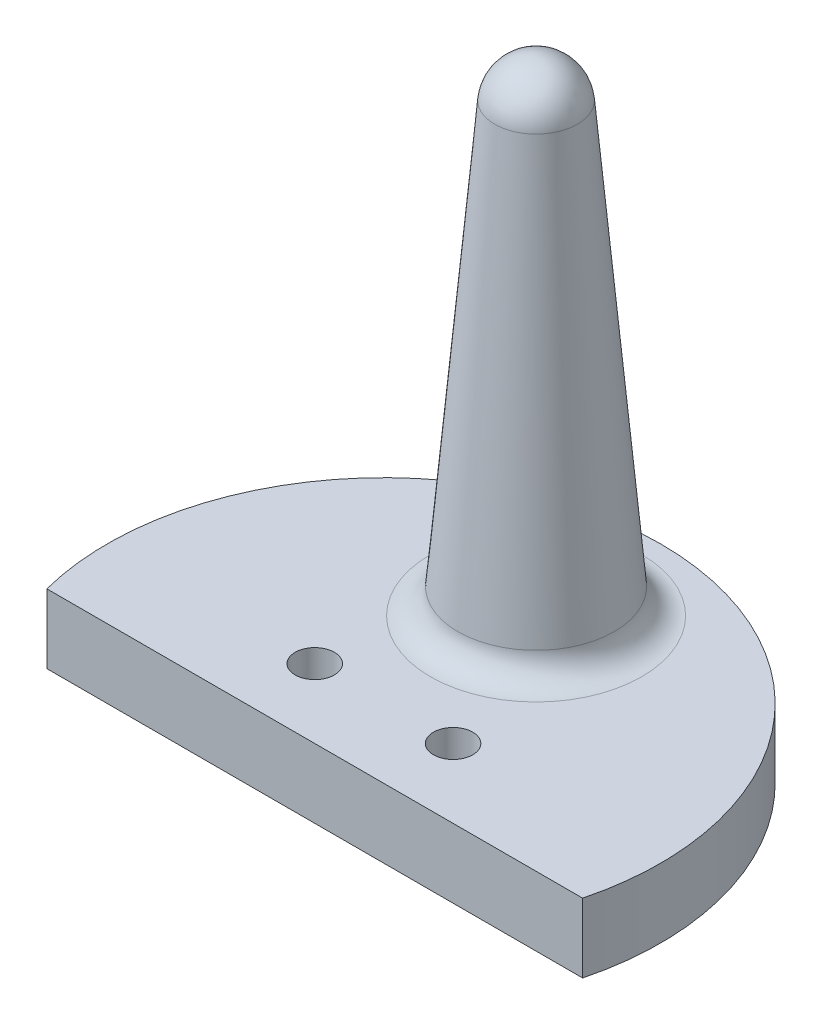
SolidWorks part; units mm, degrees
ref_plane "Front Plane" through (0, 0, 0) normal (0, 0, 1) x (1, 0, 0)
ref_plane "Top Plane" through (0, 0, 0) normal (0, 1, 0) x (1, 0, 0)
ref_plane "Right Plane" through (0, 0, 0) normal (1, 0, 0) x (0, 0, -1)
sketch "Sketch1" plane through (0, 0, 0) normal (0, 1, 0) x (1, 0, 0)
  line L0 (-19.3649, -5) -> (19.3649, -5)
  arc A0 (19.3649, -5) -> (-19.3649, -5) centre (0, 0) ccw
  circle A1 centre (-5, 0) radius 1.42
  circle A2 centre (5, 0) radius 1.42
  dimension "D3" = 40
  dimension "D4" = 5
  dimension "D5" = 2.84
  dimension "D6" = 2.84
  dimension "D1" = 5
  dimension "D2" = 5
extrude "Boss-Extrude1" add sketch "Sketch1" along normal blind 5
ref_plane "Plane1" through (0, 0, -11) normal (0, 0, 1) x (1, 0, 0)
sketch "Sketch2" plane through (0, 0, -11) normal (0, 0, 1) x (1, 0, 0)
  line L0 (0, 5) -> (0, 40)
  line L1 (-19.3649, 5) -> (19.3649, 5) construction
  line L2 (-2.9886, 37.2615) -> (-5.8111, 5)
  line L3 (-5.8111, 5) -> (0, 5)
  arc A0 (0, 40) -> (-2.9886, 37.2615) centre (0, 37) ccw
  dimension "D2" = 3
  dimension "D1" = 35
  dimension "D3" = 85
revolve "Revolve1" add sketch "Sketch2" angle 360 about L0
fillet "Fillet1" radius 2 1 edges at (0, 5, -16.8111)
